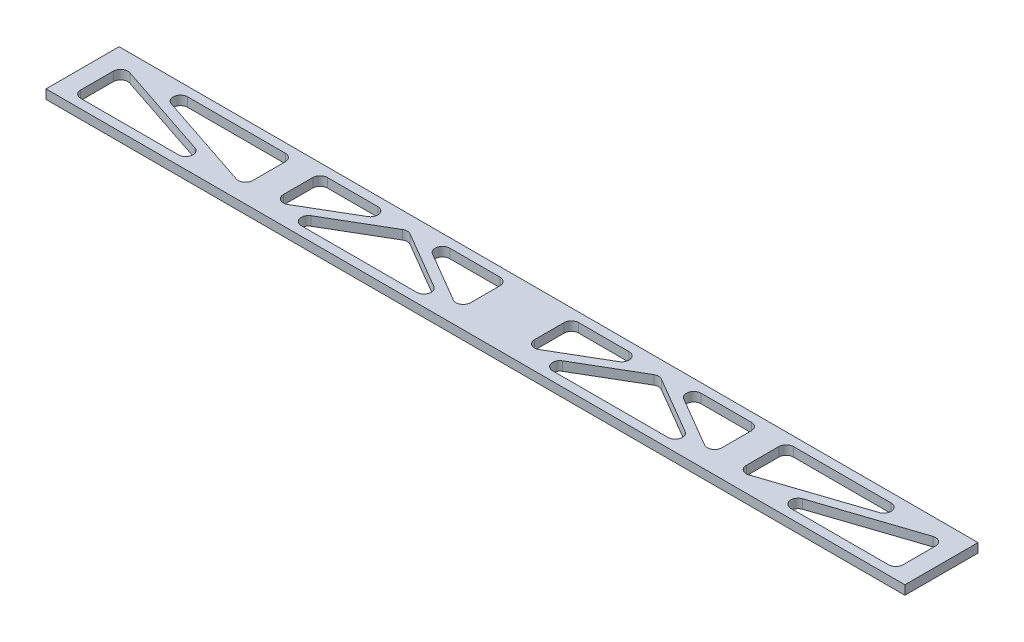
SolidWorks part; units mm, degrees
material "Plywood"
ref_plane "Front Plane" through (0, 0, 0) normal (0, 0, 1) x (1, 0, 0)
ref_plane "Top Plane" through (0, 0, 0) normal (0, 1, 0) x (1, 0, 0)
ref_plane "Right Plane" through (0, 0, 0) normal (1, 0, 0) x (0, 0, -1)
sketch "Sketch1" plane through (0, 0, 0) normal (0, 1, 0) x (1, 0, 0)
  line L1 (149.225, -12.7) -> (-149.225, -12.7)
  line L2 (149.225, -12.7) -> (149.225, 12.7)
  line L3 (149.225, 12.7) -> (-149.225, 12.7)
  line L4 (-149.225, -12.7) -> (-149.225, 12.7)
  point P0 (0, 12.7)
  point P6 (-149.225, 0)
  dimension "D1" = 25.4
  dimension "D2" = 298.45
extrude "Boss-Extrude1" add sketch "Sketch1" along normal blind 3.175
sketch "Sketch2" plane through (0, 3.175, 0) normal (0, 1, 0) x (1, 0, 0)
  line L0 (149.225, -12.7) -> (149.225, 12.7) construction
  line L2 (-149.225, 12.7) -> (-149.225, -12.7) construction
  line L4 (149.225, -12.7) -> (149.225, 12.7)
  line L6 (-149.225, 12.7) -> (-149.225, -12.7)
  line L8 (149.225, 9.525) -> (-149.225, 9.525)
  line L9 (-149.225, -9.525) -> (149.225, -9.525)
  line L10 (-142.875, 9.525) -> (-142.875, -9.525)
  line L11 (-80.9625, 9.525) -> (-80.9625, -9.525) construction
  line L12 (142.875, 9.525) -> (142.875, -9.525)
  line L13 (0, -9.525) -> (0, 9.525) construction
  line L14 (11.1125, 9.525) -> (11.1125, -9.525)
  line L15 (-11.1125, 9.525) -> (-11.1125, -9.525)
  line L16 (-85.725, 9.525) -> (-85.725, -9.525)
  line L17 (-76.2, 9.525) -> (-76.2, -9.525)
  line L18 (80.9625, 9.525) -> (80.9625, -9.525) construction
  line L19 (85.725, 9.525) -> (85.725, -9.525)
  line L20 (76.2, 9.525) -> (76.2, -9.525)
  line L21 (-76.2, -9.525) -> (-43.6562, 9.525)
  line L22 (-43.6562, 9.525) -> (-11.1125, -9.525)
  line L23 (-85.725, -9.525) -> (-142.875, 9.525)
  line L24 (11.1125, -9.525) -> (43.6562, 9.525)
  line L25 (43.6562, 9.525) -> (76.2, -9.525)
  line L26 (85.725, -9.525) -> (142.875, 9.525)
  line L27 (-85.223, -8.019) -> (-142.373, 11.031)
  line L28 (-75.398, -10.895) -> (-43.6562, 7.6855)
  line L29 (-43.6562, 7.6855) -> (-11.9145, -10.895)
  line L30 (11.9145, -10.895) -> (43.6562, 7.6855)
  line L31 (43.6562, 7.6855) -> (75.398, -10.895)
  line L32 (86.227, -11.031) -> (143.377, 8.019)
  line L33 (-86.227, -11.031) -> (-143.377, 8.019)
  line L34 (-77.002, -8.155) -> (-43.6562, 11.3645)
  line L35 (-43.6562, 11.3645) -> (-10.3105, -8.155)
  line L36 (10.3105, -8.155) -> (43.6562, 11.3645)
  line L37 (43.6562, 11.3645) -> (77.002, -8.155)
  line L38 (85.223, -8.019) -> (142.373, 11.031)
  dimension "D1" = 3.175
  dimension "D2" = 3.175
  dimension "D3" = 6.35
  dimension "D4" = 6.35
  dimension "D11" = 4.7625
  dimension "D12" = 4.7625
  dimension "D8" = 9.525
  dimension "D9" = 4.7625
  dimension "D7" = 63.5
  dimension "D10" = 63.5
  dimension "D5" = 22.225
  dimension "D6" = 11.1125
  dimension "D13" = 1.5875
  dimension "D14" = 1.5875
extrude "Cut-Extrude1" cut sketch "Sketch2" against normal through all contours L9 L33 L10 | L27 L16 L8 | L17 L34 L8 | L29 L28 L9 | L8 L35 L15 | L14 L36 L8 | L31 L30 L9 | L8 L37 L20 | L19 L38 L8 | L32 L9 L12
fillet "Fillet1" radius 2.54 30 edges at (-14.2549, 1.5875, 9.525) (-73.0576, 1.5875, 9.525) (-43.6562, 1.5875, -7.6855) (-11.1125, 1.5875, 7.6855) (-40.5138, 1.5875, -9.525) (-11.1125, 1.5875, -9.525) (-46.7987, 1.5875, -9.525) (-76.2, 1.5875, 7.6855) (-76.2, 1.5875, -9.525) (73.0576, 1.5875, 9.525) (14.2549, 1.5875, 9.525) (43.6562, 1.5875, -7.6855) (142.875, 1.5875, -7.8516) (142.875, 1.5875, 9.525) (90.7451, 1.5875, 9.525) (40.5138, 1.5875, -9.525) (11.1125, 1.5875, 7.6855) (11.1125, 1.5875, -9.525) (76.2, 1.5875, 7.6855) (46.7987, 1.5875, -9.525) (76.2, 1.5875, -9.525) (137.8549, 1.5875, -9.525) (85.725, 1.5875, 7.8516) (85.725, 1.5875, -9.525) (-137.8549, 1.5875, -9.525) (-85.725, 1.5875, 7.8516) (-85.725, 1.5875, -9.525) (-90.7451, 1.5875, 9.525) (-142.875, 1.5875, 9.525) (-142.875, 1.5875, -7.8516)
move or copy body "Body-Move/Copy1" [suppressed] bodies to move or copy 102 parameters "D1"=0, "D2"=0, "D3"=0
move or copy body "Body-Move/Copy2" [suppressed] bodies to move or copy 103 parameters "D1"=0, "D2"=0, "D3"=0
move or copy body "Body-Move/Copy3" [suppressed] bodies to move or copy 104 parameters "D1"=0, "D2"=0, "D3"=0
equation "\"D10@Sketch2\"=\"D7@Sketch2\""
equation "\"D6@Sketch2\"=\"D5@Sketch2\"/2"
